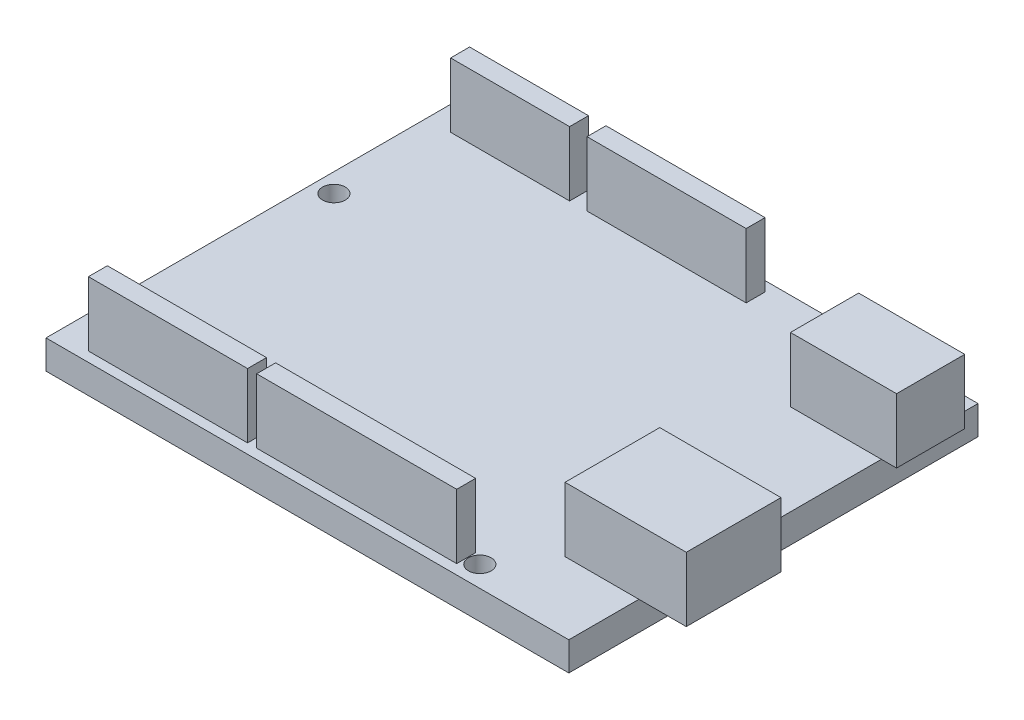
SolidWorks part; units mm, degrees
material "Silicon"
ref_plane "Front Plane" through (0, 0, 0) normal (0, 0, 1) x (1, 0, 0)
ref_plane "Top Plane" through (0, 0, 0) normal (0, 1, 0) x (1, 0, 0)
ref_plane "Right Plane" through (0, 0, 0) normal (1, 0, 0) x (0, 0, -1)
sketch "Sketch1" plane through (0, 0, 0) normal (0, 1, 0) x (1, 0, 0)
  line L0 (0, 0) -> (0, 54) construction
  line L1 (-34.5, 27) -> (34.5, 27) construction
  line L3 (-34.5, 54) -> (34.5, 54)
  line L4 (-34.5, 54) -> (-34.5, 0)
  line L5 (-34.5, 0) -> (34.5, 0)
  line L6 (34.5, 54) -> (34.5, 0)
  line L7 (-34.5, 54) -> (34.5, 0) construction
  line L8 (-34.5, 0) -> (34.5, 54) construction
  circle A0 centre (-32, 7.5) radius 1.5
  circle A1 centre (-32, 35.5) radius 1.5
  circle A2 centre (19, 51.5) radius 1.5
  circle A3 centre (20, 2.75) radius 1.5
  point P5 (0, 27)
  point P6 (0, 27)
  point P7 (0, 27)
  point P20 (-29.8252, 40.4449)
  point P21 (0, 0)
  dimension "D3" = 3
  dimension "D4" = 3
  dimension "D5" = 3
  dimension "D6" = 3
  dimension "D1" = 54
  dimension "D2" = 69
  dimension "D7" = 28
  dimension "D8" = 2.5
  dimension "D9" = 7.5
  dimension "D10" = 2.75
  dimension "D11" = 15.5
  dimension "D12" = 2.5
  dimension "D13" = 14.5
extrude "Boss-Extrude1" add sketch "Sketch1" along normal blind 3.8
sketch "Sketch2" plane through (0, 3.8, 0) normal (0, 1, 0) x (1, 0, 0)
  line L0 (34.5, 54) -> (-34.5, 54) construction
  line L1 (24.75, 21.75) -> (40.75, 21.75)
  line L2 (24.75, 21.75) -> (24.75, 9.25)
  line L3 (24.75, 9.25) -> (40.75, 9.25)
  line L4 (40.75, 21.75) -> (40.75, 9.25)
  line L5 (24.75, 21.75) -> (40.75, 9.25) construction
  line L6 (24.75, 9.25) -> (40.75, 21.75) construction
  line L7 (22.5, 50.25) -> (36.5, 50.25)
  line L8 (22.5, 50.25) -> (22.5, 41.25)
  line L9 (22.5, 41.25) -> (36.5, 41.25)
  line L10 (36.5, 50.25) -> (36.5, 41.25)
  line L11 (22.5, 50.25) -> (36.5, 41.25) construction
  line L12 (22.5, 41.25) -> (36.5, 50.25) construction
  line L13 (-30.2, 1.3) -> (-9.2, 1.3)
  line L14 (-30.2, 1.3) -> (-30.2, 3.8)
  line L15 (-30.2, 3.8) -> (-9.2, 3.8)
  line L16 (-9.2, 1.3) -> (-9.2, 3.8)
  line L17 (-30.2, 1.3) -> (-9.2, 3.8) construction
  line L18 (-30.2, 3.8) -> (-9.2, 1.3) construction
  line L19 (-8, 1.3) -> (18.4, 1.3)
  line L20 (-8, 1.3) -> (-8, 3.8)
  line L21 (-8, 3.8) -> (18.4, 3.8)
  line L22 (18.4, 1.3) -> (18.4, 3.8)
  line L23 (-8, 1.3) -> (18.4, 3.8) construction
  line L24 (-8, 3.8) -> (18.4, 1.3) construction
  line L25 (-15.6, 52.7) -> (-31.3, 52.7)
  line L26 (-15.6, 52.7) -> (-15.6, 50.2)
  line L27 (-15.6, 50.2) -> (-31.3, 50.2)
  line L28 (-31.3, 52.7) -> (-31.3, 50.2)
  line L29 (-15.6, 52.7) -> (-31.3, 50.2) construction
  line L30 (-15.6, 50.2) -> (-31.3, 52.7) construction
  line L31 (-13.3, 52.7) -> (7.7, 52.7)
  line L32 (-13.3, 52.7) -> (-13.3, 50.2)
  line L33 (-13.3, 50.2) -> (7.7, 50.2)
  line L34 (7.7, 52.7) -> (7.7, 50.2)
  line L35 (-13.3, 52.7) -> (7.7, 50.2) construction
  line L36 (-13.3, 50.2) -> (7.7, 52.7) construction
  line L37 (-34.5, 0) -> (34.5, 0) construction
  line L39 (34.5, 0) -> (34.5, 54) construction
  line L40 (-34.5, 54) -> (-34.5, 0) construction
  point P0 (32.75, 15.5)
  point P5 (29.5, 45.75)
  point P10 (-19.7, 2.55)
  point P15 (5.2, 2.55)
  point P20 (-23.45, 51.45)
  point P25 (-2.8, 51.45)
  point P36 (-8, 2.55)
  dimension "D1" = 12.5
  dimension "D2" = 16
  dimension "D3" = 14
  dimension "D4" = 9
  dimension "D5" = 3.75
  dimension "D6" = 9.25
  dimension "D7" = 6.25
  dimension "D8" = 2
  dimension "D9" = 2.5
  dimension "D10" = 2.5
  dimension "D11" = 21
  dimension "D12" = 1.2
  dimension "D13" = 26.4
  dimension "D14" = 1.3
  dimension "D15" = 4.3
  dimension "D16" = 3.2
  dimension "D17" = 15.7
  dimension "D18" = 2.3
  dimension "D19" = 1.3
  dimension "D20" = 21
extrude "Boss-Extrude2" add sketch "Sketch2" along normal blind 8.5
